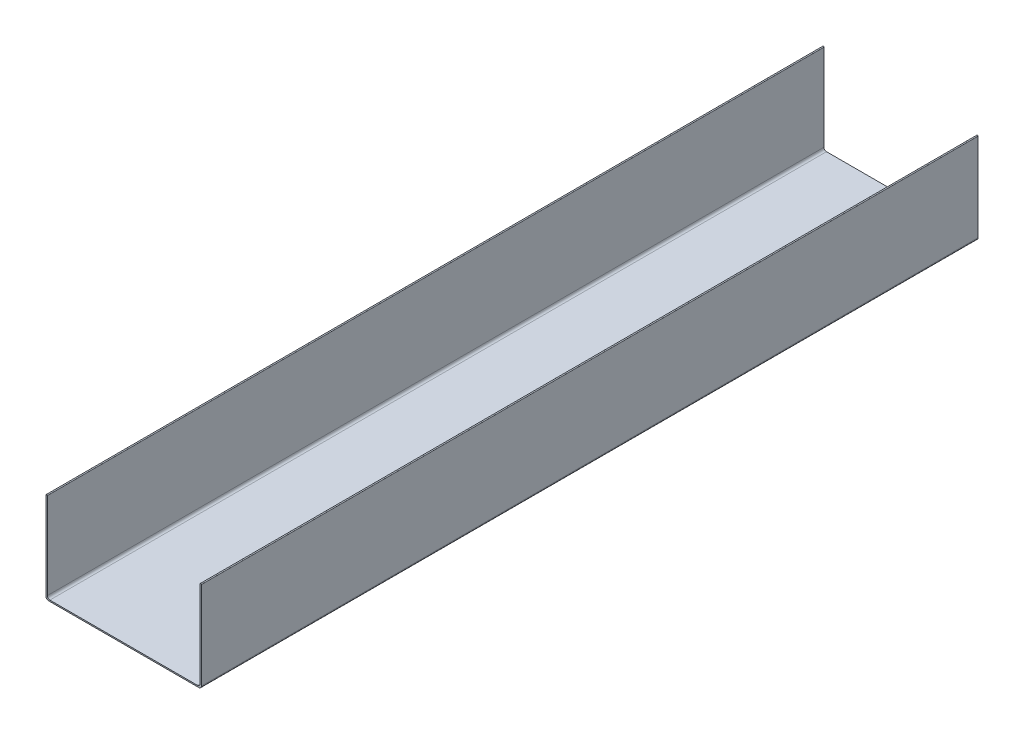
SolidWorks part; units mm, degrees
ref_plane "Front Plane" through (0, 0, 0) normal (0, 0, 1) x (1, 0, 0)
ref_plane "Top Plane" through (0, 0, 0) normal (0, 1, 0) x (1, 0, 0)
ref_plane "Right Plane" through (0, 0, 0) normal (1, 0, 0) x (0, 0, -1)
sketch "Sketch1" plane through (0, 0, 0) normal (0, 0, 1) x (1, 0, 0)
  line L0 (0, 0) -> (0, -86.36)
  line L5 (2.54, -88.9) -> (149.86, -88.9)
  line L6 (152.4, -86.36) -> (152.4, 0)
  line L7 (-1.27, 0) -> (-1.27, -87.63)
  line L8 (1.27, -90.17) -> (151.13, -90.17)
  line L9 (153.67, -87.63) -> (153.67, 0)
  line L10 (0, -88.9) -> (152.4, -88.9) construction
  line L11 (152.4, -88.9) -> (152.4, 0) construction
  line L12 (-1.27, -90.17) -> (153.67, -90.17) construction
  line L13 (153.67, -90.17) -> (153.67, 0) construction
  line L14 (0, 0) -> (0, -88.9) construction
  line L15 (-1.27, 0) -> (-1.27, -90.17) construction
  arc A0 (0, 0) -> (-1.27, 0) centre (-0.635, 0) ccw
  arc A1 (152.4, 0) -> (153.67, 0) centre (153.035, 0) cw
  arc A2 (149.86, -88.9) -> (152.4, -86.36) centre (149.86, -86.36) ccw
  arc A3 (151.13, -90.17) -> (153.67, -87.63) centre (151.13, -87.63) ccw
  arc A4 (0, -86.36) -> (2.54, -88.9) centre (2.54, -86.36) ccw
  arc A5 (-1.27, -87.63) -> (1.27, -90.17) centre (1.27, -87.63) ccw
  point P4 (169.3107, 44.4485)
  point P6 (14.0711, 39.9689)
  point P8 (0, 0)
  point P19 (152.4, -88.9)
  dimension "D4" = 2.54
  dimension "D1" = 152.4
  dimension "D2" = 88.9
  dimension "D3" = 1.27
extrude "Boss-Extrude1" add sketch "Sketch1" along normal blind 774.7
